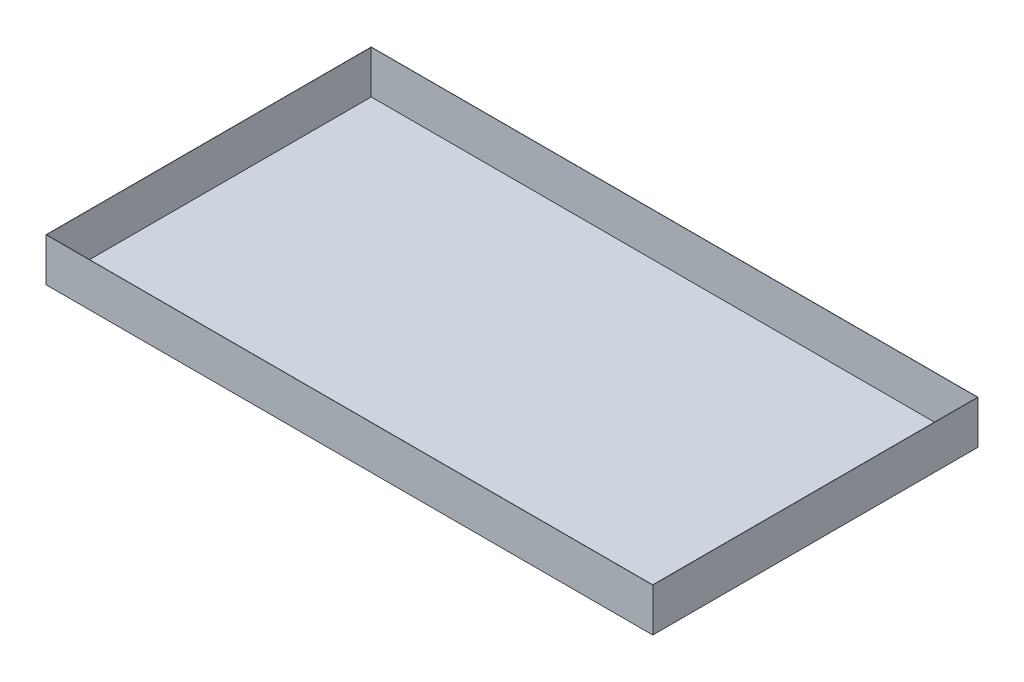
SolidWorks part; units mm, degrees
ref_plane "前视基准面" through (0, 0, 0) normal (0, 0, 1) x (1, 0, 0)
ref_plane "上视基准面" through (0, 0, 0) normal (0, 1, 0) x (1, 0, 0)
ref_plane "右视基准面" through (0, 0, 0) normal (1, 0, 0) x (0, 0, -1)
sketch "草图1" plane through (0, 0, 0) normal (0, 1, 0) x (1, 0, 0)
  line L1 (14000, -7500) -> (-14000, -7500)
  line L2 (14000, -7500) -> (14000, 7500)
  line L3 (14000, 7500) -> (-14000, 7500)
  line L4 (-14000, -7500) -> (-14000, 7500)
  line L5 (14000, -7500) -> (-14000, 7500) construction
  line L6 (14000, 7500) -> (-14000, -7500) construction
  point P0 (0, 0)
  dimension "D1" = 28000
  dimension "D2" = 15000
extrude "凸台-拉伸1" add sketch "草图1" along normal blind 10
sketch "草图3" plane through (0, 0, 0) normal (0, -1, 0) x (1, 0, 0)
  line L0 (-14000, 7500) -> (14000, 7500) construction
  line L1 (14000, -7500) -> (-14000, -7500)
  line L2 (14000, -7500) -> (14000, 7500)
  line L3 (14000, 7500) -> (-14000, 7500)
  line L4 (-14000, -7500) -> (-14000, 7500)
  line L5 (14010, 7510) -> (-14010, 7510)
  line L6 (-14010, -7510) -> (-14010, 7510)
  line L7 (14010, -7510) -> (-14010, -7510)
  line L8 (14010, -7510) -> (14010, 7510)
  point P0 (0, 0)
  dimension "D1" = 10
extrude "凸台-拉伸2" add sketch "草图3" against normal blind 2000
